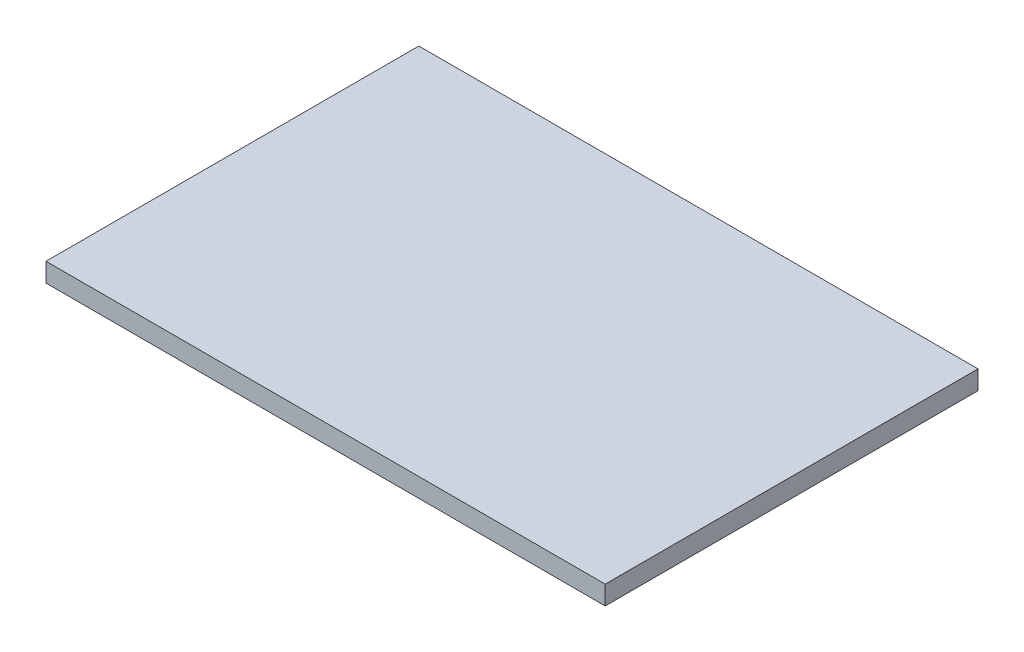
SolidWorks part; units mm, degrees
ref_plane "Alzado" through (0, 0, 0) normal (0, 0, 1) x (1, 0, 0)
ref_plane "Planta" through (0, 0, 0) normal (0, 1, 0) x (1, 0, 0)
ref_plane "Vista lateral" through (0, 0, 0) normal (1, 0, 0) x (0, 0, -1)
sketch "Croquis1" plane through (0, 0, 0) normal (0, 1, 0) x (1, 0, 0)
  line L1 (-375, -250) -> (375, -250)
  line L2 (-375, -250) -> (-375, 250)
  line L3 (-375, 250) -> (375, 250)
  line L4 (375, -250) -> (375, 250)
  line L5 (-375, -250) -> (375, 250) construction
  line L6 (-375, 250) -> (375, -250) construction
  point P0 (0, 0)
  dimension "D1" = 500
  dimension "D2" = 750
extrude "Saliente-Extruir1" add sketch "Croquis1" along normal blind 25.4
